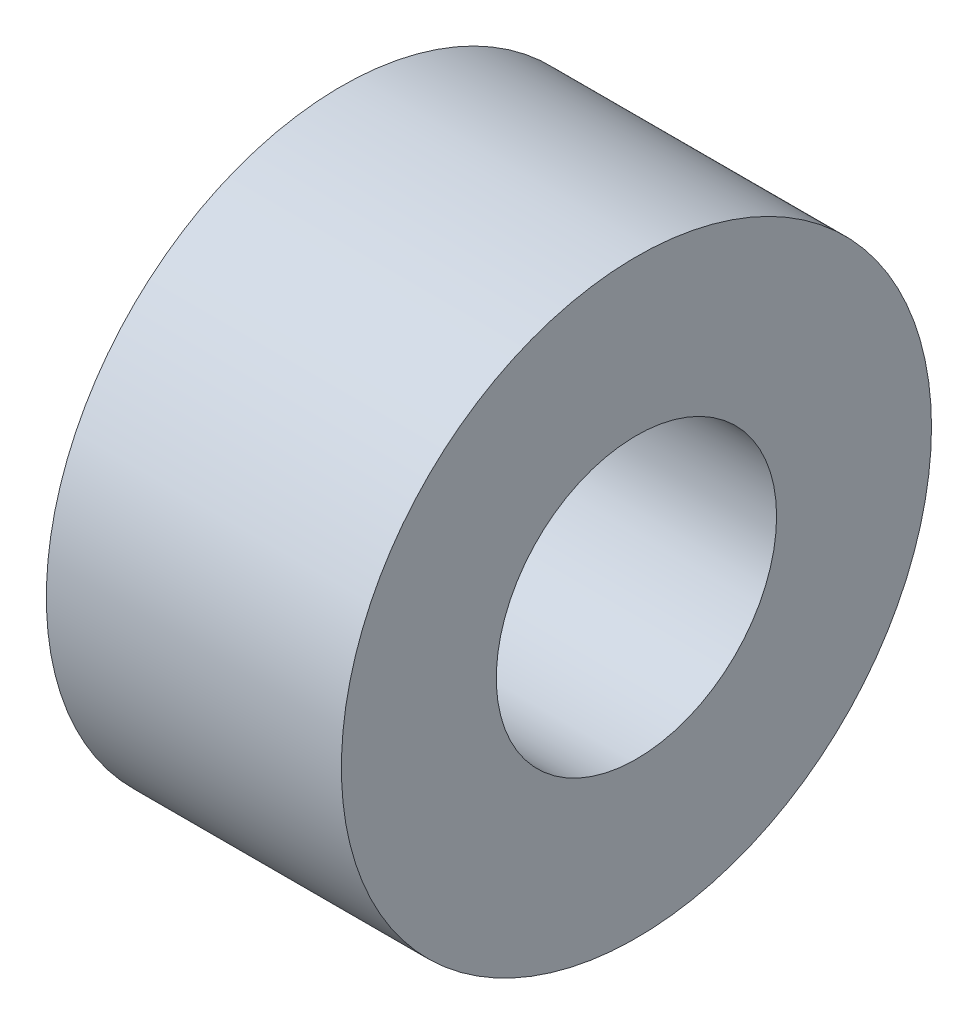
SolidWorks part; units mm, degrees
ref_plane "Front Plane" through (0, 0, 0) normal (0, 0, 1) x (1, 0, 0)
ref_plane "Top Plane" through (0, 0, 0) normal (0, 1, 0) x (1, 0, 0)
ref_plane "Right Plane" through (0, 0, 0) normal (1, 0, 0) x (0, 0, -1)
sketch "Sketch1" plane through (0, 0, 0) normal (1, 0, 0) x (0, 0, -1)
  circle A0 centre (0, 0) radius 10
  circle A1 centre (0, 0) radius 4.75
  dimension "D1" = 9.5
  dimension "D2" = 20
extrude "Boss-Extrude1" add sketch "Sketch1" along normal blind 10
